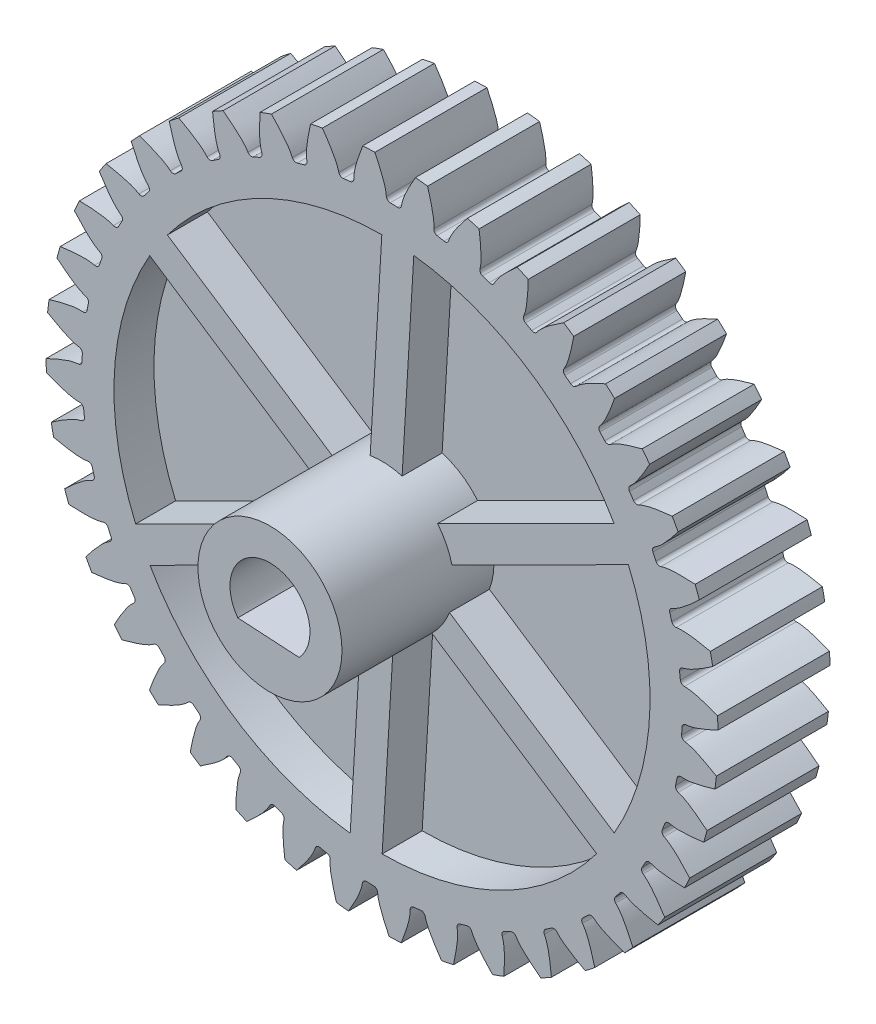
SolidWorks part; units mm, degrees
material "PVC rigide"
ref_plane "Plan1" through (0, 0, 0) normal (0, 0, 1) x (1, 0, 0)
ref_plane "Plan2" through (0, 0, 0) normal (0, 1, 0) x (1, 0, 0)
ref_plane "Plan3" through (0, 0, 0) normal (1, 0, 0) x (0, 0, -1)
sketch "Esquisse1" plane through (0, 0, 0) normal (0, 0, 1) x (1, 0, 0)
  circle A0 centre (0, 0) radius 18.75
  dimension "Dp" = 37.5
sketch "Esquisse2" plane through (0, 0, 0) normal (0, 0, 1) x (1, 0, 0)
  line L0 (0, 0) -> (20.9839, 0.823) construction
  line L1 (18.7918, -0.28) -> (18.8069, 0.7376) construction
  line L2 (0, 0) -> (18.7918, -0.28) construction
  line L3 (0, 0) -> (20, 0) construction
  line L4 (0, 0) -> (20.9953, 0.4431) construction
  line L5 (20, 0) -> (20.9953, 0.4431) construction
  line L6 (17.5924, 0.0359) -> (16.6107, 0.5084) construction
  line L7 (17.0703, 1.0681) -> (17.1016, 0.2721)
  circle A0 centre (0, 0) radius 18.7938 construction
  circle A1 centre (0, 0) radius 20 construction
  circle A2 centre (0, 0) radius 21 construction
  arc A3 (20.9655, 1.2026) -> (20.9953, 0.4431) centre (0, 0) cw
  spline S0 degree 3 poles (17.1016, 0.2721) (17.2634, 0.1915) (17.7935, -0.0729) (18.7916, -0.4156) (19.9703, -0.0395) (20.6687, 0.2893) (20.9953, 0.4431) knots 0 0 0 0 0.132388 0.433806 0.735224 1 1 1 1
  spline S1 degree 3 poles (17.0703, 1.0681) (17.2253, 1.1612) (17.7331, 1.4663) (18.7014, 1.8861) (19.9058, 1.6035) (20.6279, 1.3304) (20.9655, 1.2026) knots 0 0 0 0 0.132388 0.433806 0.735224 1 1 1 1
  dimension "Db" = 37.5877
  dimension "Dn" = 40
  dimension "Dt" = 42
  dimension "Tn" = 0.854
  dimension "Tt" = 2.063
  dimension "Ts" = 2.246
extrude "Base-Extrusion" add sketch "Esquisse1" along normal mid plane 7
sketch "Esquisse8" plane through (0, 0, -3.5) normal (0, 0, -1) x (-1, 0, 0)
  circle A2 centre (0, 0) radius 16.75
  circle A3 centre (0, 0) radius 16.75
  dimension "D1" = 2
extrude "Enlèv. mat.-Extru.4" cut sketch "Esquisse8" against normal blind 2.5
mirror "Symétrie1" about plane through (0, 0, 0) normal (0, 0, 1) of "Enlèv. mat.-Extru.4"
ref_axis "Axe1" through (0, 0, -50) along (0, 0, 1)
ref_plane "Plan median" through (0, 0, 0) normal (0, 0, -1) x (-1, 0, 0)
extrude "Boss.-Extru.1" add sketch "Esquisse2" along normal mid plane 7
fillet "Congé1" radius 0.25 4 edges at (18.7479, -0.279, 0) (18.6685, 1.7465, 0)
pattern_circular "Répétition circulaire1" count 40 over 360 about axis through (0, 0, -50) along (0, 0, 1) of "Boss.-Extru.1", "Congé1"
sketch "Esquisse3" plane through (0, 0, 0) normal (0, 0, 1) x (1, 0, 0)
  line L3 (-2.0121, -1.4837) -> (1.823, -1.7107) construction
  line L4 (-2.0121, -1.4837) -> (1.823, -1.7107)
  arc A3 (1.823, -1.7107) -> (-2.0121, -1.4837) centre (0, 0) ccw
extrude "Enlèv. mat.-Extru.2" cut sketch "Esquisse3" against normal through all both and the other way through all
sketch "Esquisse4" plane through (0, 0, -3.5) normal (0, 0, -1) x (-1, 0, 0)
  line L1 (-1.823, -1.7107) -> (2.0121, -1.4837) construction
  line L2 (-1.823, -1.7107) -> (2.0121, -1.4837)
  circle A0 centre (0, 0) radius 20 construction
  circle A1 centre (0, 0) radius 20
  arc A3 (2.0121, -1.4837) -> (-1.823, -1.7107) centre (0, 0) ccw construction
  arc A4 (2.0121, -1.4837) -> (-1.823, -1.7107) centre (0, 0) ccw
extrude "Cylindre primitif" [suppressed] add sketch "Esquisse4" along normal up to surface (10 mm away)
ref_plane "Plan médian dent" through (0, 0, 0) normal (-0.0392, 0.9992, 0) x (-0.9992, -0.0392, 0)
ref_plane "Planmédian creux" through (0, 0, 0) normal (-0.1175, 0.9931, 0) x (-0.9931, -0.1175, 0)
sketch "Esquisse5" plane through (0, 0, 3.5) normal (0, 0, 1) x (1, 0, 0)
  line L4 (-2.0121, -1.4837) -> (1.823, -1.7107) construction
  line L5 (-2.0121, -1.4837) -> (1.823, -1.7107)
  arc A3 (-2.0121, -1.4837) -> (1.823, -1.7107) centre (0, 0) ccw construction
  arc A5 (1.823, -1.7107) -> (-2.0121, -1.4837) centre (0, 0) ccw
  circle A7 centre (0, 0) radius 4.5
  dimension "D1" = 2
extrude "Boss.-Extru.2" add sketch "Esquisse5" along normal blind 7 and the other way up to surface
sketch "Esquisse7" plane through (0, 0, -3.5) normal (0, 0, -1) x (-1, 0, 0)
  line L0 (0.2659, -4.4921) -> (0.9898, -16.7207)
  line L2 (-3.7573, -2.4764) -> (-13.9857, -9.2176)
  line L3 (-4.0233, 2.0158) -> (-14.9755, 7.5031)
  line L4 (-0.2659, 4.4921) -> (-0.9898, 16.7207)
  line L5 (3.7573, 2.4764) -> (13.9857, 9.2176)
  line L6 (4.0233, -2.0158) -> (14.9755, -7.5031)
  line L7 (-1.823, -1.7107) -> (2.0121, -1.4837) construction
  circle A1 centre (0, 0) radius 4.5 construction
  circle A2 centre (0, 0) radius 16.75 construction
  point P19 (0, 0)
  dimension "D1" = 6
rib "Nervure1" sketch "Esquisse7" sketch "Esquisse7" thickness 2 extrusion direction normal to sketch draft on no parameters "D1"=2
mirror "Symétrie2" about plane through (0, 0, 0) normal (0, 0, 1) of "Nervure1"
sketch "Esquisse6" plane through (-0.0946, -1.5972, 0) normal (0.0591, 0.9983, 0) x (0.9983, -0.0591, 0)
  line L0 (-1, -3.5) -> (1, -3.5) construction
  line L3 (-1.9209, -3.5) -> (1.9209, -10.5) construction
  line L5 (-1, -3.5) -> (1, -3.5) construction
  line L6 (1.9209, 3.5) -> (-1.9209, 3.5)
  line L7 (1.9209, 3.5) -> (-1.9209, 3.5) construction
  line L12 (-1.9209, 3.5) -> (-1.9209, -10.5)
  line L13 (-1.9209, 3.5) -> (-1.9209, -10.5) construction
  line L22 (1.9209, -10.5) -> (1.9209, 3.5)
  line L23 (-1.9209, -10.5) -> (1.9209, -10.5)
  line L25 (1.9209, -10.5) -> (1.9209, 3.5) construction
  line L27 (-1.9209, -10.5) -> (1.9209, -10.5) construction
  circle A0 centre (0, -7) radius 1.65
  dimension "D2" = 3.3
  dimension "D1" = 0
extrude "Enlèv. mat.-Extru.3" [suppressed] cut sketch "Esquisse6" against normal up to next
equation "\"D1@Boss.-Extru.1\"=\"D1@Base-Extrusion\""
equation "\"D1@Plan median\"=\"D1@Base-Extrusion\"/2"
equation "\"D1@Planmédian creux\"=360/2/\"D1@Répétition circulaire1\""
